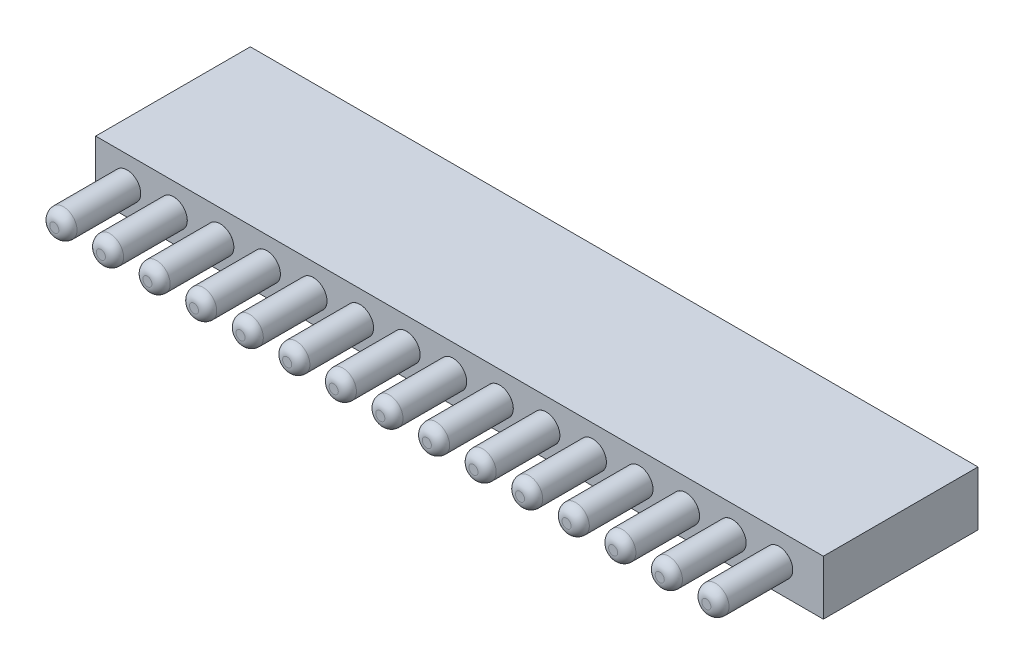
SolidWorks part; units mm, degrees
ref_plane "Front Plane" through (0, 0, 0) normal (0, 0, 1) x (1, 0, 0)
ref_plane "Top Plane" through (0, 0, 0) normal (0, 1, 0) x (1, 0, 0)
ref_plane "Right Plane" through (0, 0, 0) normal (1, 0, 0) x (0, 0, -1)
sketch "Sketch1" plane through (0, 0, 0) normal (0, 0, 1) x (1, 0, 0)
  circle A0 centre (0, 0) radius 0.75
  circle A1 centre (2.56, 0) radius 0.75
  circle A2 centre (5.12, 0) radius 0.75
  circle A3 centre (7.68, 0) radius 0.75
  circle A4 centre (10.24, 0) radius 0.75
  circle A5 centre (12.8, 0) radius 0.75
  circle A6 centre (15.36, 0) radius 0.75
  circle A7 centre (17.92, 0) radius 0.75
  circle A8 centre (20.48, 0) radius 0.75
  circle A9 centre (23.04, 0) radius 0.75
  circle A10 centre (25.6, 0) radius 0.75
  circle A11 centre (28.16, 0) radius 0.75
  circle A12 centre (30.72, 0) radius 0.75
  circle A13 centre (33.28, 0) radius 0.75
  circle A14 centre (35.84, 0) radius 0.75
  dimension "D1" = 1.5
  dimension "D2" = 15
extrude "Boss-Extrude1" add sketch "Sketch1" along normal blind 4
fillet "Fillet1" radius 0.5 1 edges at (0.75, 0, 4)
sketch "Sketch2" plane through (0, 0, 0) normal (0, 0, -1) x (-1, 0, 0)
  line L0 (1.7251, 0) -> (-38.2749, 0) construction
  line L1 (1.7251, 1.5) -> (-38.2749, 1.5)
  line L2 (1.7251, 1.5) -> (1.7251, -1.5)
  line L3 (1.7251, -1.5) -> (-38.2749, -1.5)
  line L4 (-38.2749, 1.5) -> (-38.2749, -1.5)
  circle A1 centre (-30.72, 0) radius 0.75 construction
  circle A2 centre (-28.16, 0) radius 0.75 construction
  circle A3 centre (-25.6, 0) radius 0.75 construction
  circle A4 centre (-23.04, 0) radius 0.75 construction
  circle A5 centre (-20.48, 0) radius 0.75 construction
  circle A6 centre (-10.24, 0) radius 0.75 construction
  circle A7 centre (-35.84, 0) radius 0.75 construction
  circle A8 centre (-33.28, 0) radius 0.75 construction
  circle A9 centre (-17.92, 0) radius 0.75 construction
  circle A10 centre (-15.36, 0) radius 0.75 construction
  circle A11 centre (-12.8, 0) radius 0.75 construction
  circle A12 centre (-10.24, 0) radius 0.75 construction
  circle A13 centre (-7.68, 0) radius 0.75 construction
  circle A14 centre (-5.12, 0) radius 0.75 construction
  circle A15 centre (-2.56, 0) radius 0.75 construction
  circle A16 centre (0, 0) radius 0.75 construction
  circle A17 centre (-30.72, 0) radius 0.75
  circle A18 centre (-28.16, 0) radius 0.75
  circle A19 centre (-25.6, 0) radius 0.75
  circle A20 centre (-23.04, 0) radius 0.75
  circle A21 centre (-20.48, 0) radius 0.75
  circle A22 centre (-10.24, 0) radius 0.75
  circle A23 centre (-35.84, 0) radius 0.75
  circle A24 centre (-33.28, 0) radius 0.75
  circle A25 centre (-17.92, 0) radius 0.75
  circle A26 centre (-15.36, 0) radius 0.75
  circle A27 centre (-12.8, 0) radius 0.75
  circle A28 centre (-10.24, 0) radius 0.75
  circle A29 centre (-7.68, 0) radius 0.75
  circle A30 centre (-5.12, 0) radius 0.75
  circle A31 centre (-2.56, 0) radius 0.75
  circle A32 centre (0, 0) radius 0.75
  point P6 (0.2434, 0)
  point P8 (-35.84, 0)
  circle M4 centre (0, 0) radius 0.75
  dimension "D1" = 3
  dimension "D2" = 40
extrude "Boss-Extrude2" add sketch "Sketch2" along normal blind 8.5 separate body contours L2 L0 A32 A31 A30 A29 A28 A27 A26 A25 A21 A20 A19 A18 A17 A24 A23 L4 L3 | L0 L2 L1 L4 A23 A24 A17 A18 A19 A20 A21 A25 A26 A27 A22 A29 A30 A31 M4
fillet "Fillet2" radius 0.5 1 edges at (3.31, 0, 4)
fillet "Fillet3" radius 0.5 1 edges at (5.87, 0, 4)
fillet "Fillet4" radius 0.5 1 edges at (8.43, 0, 4)
fillet "Fillet5" radius 0.5 1 edges at (10.99, 0, 4)
fillet "Fillet6" radius 0.5 1 edges at (13.55, 0, 4)
fillet "Fillet7" radius 0.5 1 edges at (16.11, 0, 4)
fillet "Fillet8" radius 0.5 1 edges at (18.67, 0, 4)
fillet "Fillet9" radius 0.5 1 edges at (21.23, 0, 4)
fillet "Fillet10" radius 0.5 1 edges at (23.79, 0, 4)
fillet "Fillet11" radius 0.5 1 edges at (26.35, 0, 4)
fillet "Fillet12" radius 0.5 1 edges at (28.91, 0, 4)
fillet "Fillet13" radius 0.5 1 edges at (31.47, 0, 4)
fillet "Fillet14" radius 0.5 1 edges at (34.03, 0, 4)
fillet "Fillet15" radius 0.5 1 edges at (36.59, 0, 4)
